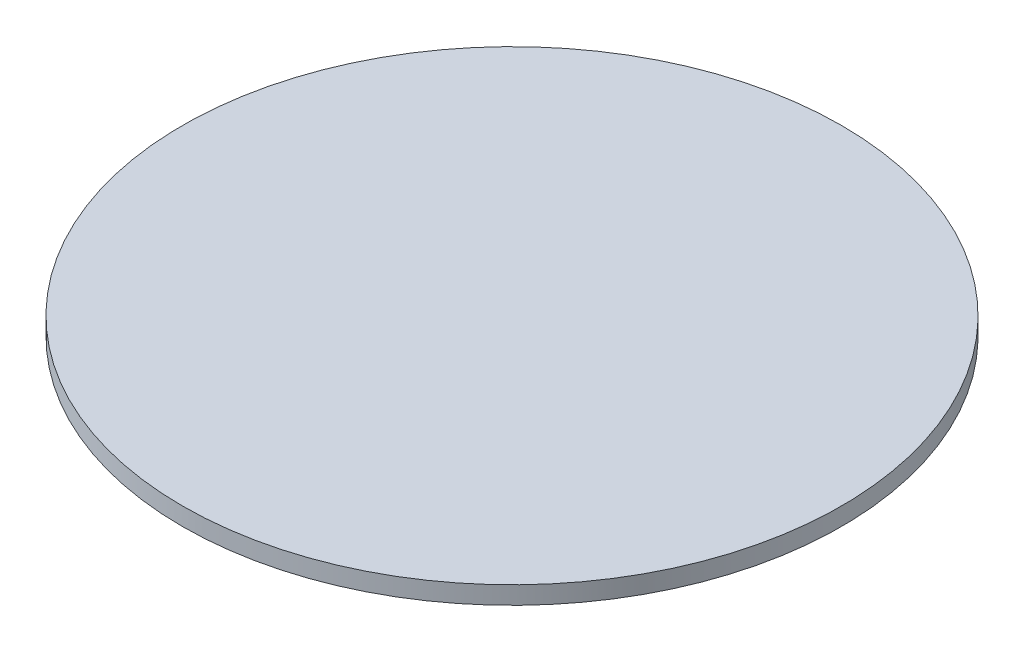
SolidWorks part; units mm, degrees
ref_plane "前视基准面" through (0, 0, 0) normal (0, 0, 1) x (1, 0, 0)
ref_plane "上视基准面" through (0, 0, 0) normal (0, 1, 0) x (1, 0, 0)
ref_plane "右视基准面" through (0, 0, 0) normal (1, 0, 0) x (0, 0, -1)
sketch "草图1" plane through (0, 0, 0) normal (0, 1, 0) x (1, 0, 0)
  circle A0 centre (0, 0) radius 18.5
  dimension "D1" = 37
extrude "凸台-拉伸1" add sketch "草图1" along normal blind 1
